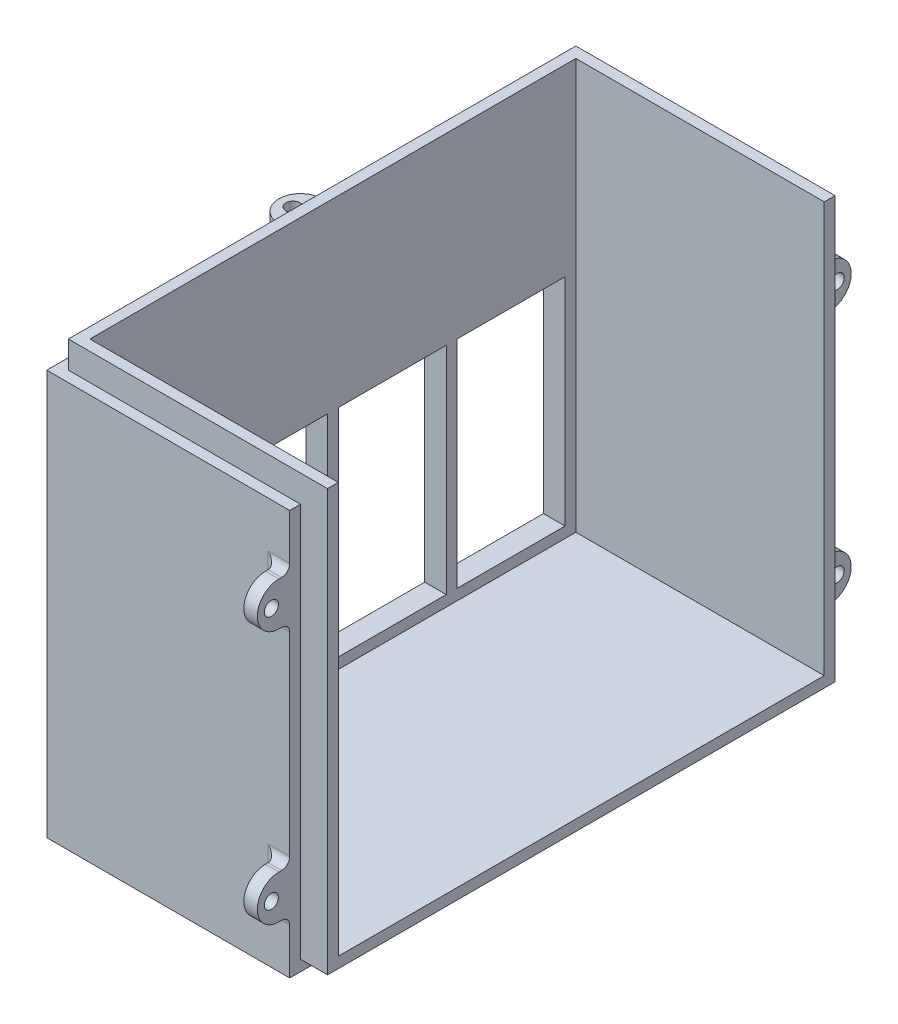
SolidWorks part; units mm, degrees
ref_plane "Front Plane" through (0, 0, 0) normal (0, 0, 1) x (1, 0, 0)
ref_plane "Top Plane" through (0, 0, 0) normal (0, 1, 0) x (1, 0, 0)
ref_plane "Right Plane" through (0, 0, 0) normal (1, 0, 0) x (0, 0, -1)
sketch "Sketch1" plane through (0, 0, 0) normal (0, 1, 0) x (1, 0, 0)
  line L1 (-25, 49) -> (25, 49)
  line L2 (-25, 49) -> (-25, -49)
  line L3 (-25, -49) -> (25, -49)
  line L4 (25, 49) -> (25, -49)
  line L5 (-25, 49) -> (25, -49) construction
  line L6 (-25, -49) -> (25, 49) construction
  point P0 (0, 0)
  dimension "D1" = 98
  dimension "D2" = 50
extrude "Boss-Extrude3" add sketch "Sketch1" along normal blind 80
sketch "Sketch4" plane through (25, 0, 0) normal (1, 0, 0) x (0, 0, -1)
  line L0 (-49, 80) -> (49, 80) construction
  line L1 (-45, 80) -> (45, 80)
  line L2 (-45, 80) -> (-45, 4)
  line L3 (-45, 4) -> (45, 4)
  line L4 (45, 80) -> (45, 4)
  line L5 (-49, 80) -> (-49, 0) construction
  line L6 (-49, 0) -> (49, 0) construction
  line L7 (49, 80) -> (49, 0) construction
  dimension "D1" = 4
  dimension "D2" = 4
  dimension "D3" = 4
extrude "Cut-Extrude2" cut sketch "Sketch4" against normal blind 46
sketch "Sketch6" plane through (0, 80, 0) normal (0, 1, 0) x (1, 0, 0)
  line L0 (-25, 49) -> (-25, -49) construction
  line L1 (25, -49) -> (-25, -49)
  line L2 (25, -49) -> (25, -47)
  line L3 (25, -47) -> (-25, -47)
  line L4 (-25, -49) -> (-25, -47)
  line L5 (25, 49) -> (-25, 49) construction
  line L6 (-25, -47) -> (-23, -47)
  line L7 (-25, -47) -> (-25, 49)
  line L8 (-25, 49) -> (-23, 49)
  line L9 (-23, -47) -> (-23, 49)
  line L10 (25, 45) -> (25, 49) construction
  line L11 (-23, 49) -> (25, 49)
  line L12 (-23, 49) -> (-23, 47)
  line L13 (-23, 47) -> (25, 47)
  line L14 (25, 49) -> (25, 47)
  line M9 (25, 45) -> (25, 49)
  line M10 (25, 49) -> (-25, 49)
  line M11 (-25, 49) -> (-25, -49)
  line M12 (-25, -49) -> (25, -49)
  line M13 (25, -49) -> (25, -45)
  dimension "D1" = 2
  dimension "D2" = 2
extrude "Cut-Extrude3" cut sketch "Sketch6" against normal blind 5 contours L9 L13 M9 M10 | L3 L9 M10 M11 | L3 M13 M11 M12
sketch "Sketch7" plane through (25, 0, 0) normal (1, 0, 0) x (0, 0, -1)
  line L0 (-49, 0) -> (49, 0) construction
  line L1 (-49, 75) -> (-47, 75)
  line L2 (-49, 75) -> (-49, 0)
  line L3 (-49, 0) -> (-47, 0)
  line L4 (-47, 75) -> (-47, 0)
  line L5 (-47, 75) -> (-47, 80) construction
  line L6 (49, 75) -> (49, 0) construction
  line L7 (-47, 0) -> (49, 0)
  line L8 (-47, 0) -> (-47, 2)
  line L9 (-47, 2) -> (49, 2)
  line L10 (49, 0) -> (49, 2)
  line L12 (49, 2) -> (47, 2)
  line L13 (49, 2) -> (49, 75)
  line L14 (49, 75) -> (47, 75)
  line L15 (47, 2) -> (47, 75)
  line M7 (-49, 0) -> (49, 0)
  line M8 (49, 0) -> (49, 75)
  line M9 (49, 75) -> (47, 75)
  dimension "D1" = 0
  dimension "D2" = 2
extrude "Cut-Extrude4" cut sketch "Sketch7" against normal blind 5 contours L9 L4 M7 M8 | L15 L9 M8 M9
sketch "Sketch10" plane through (20, 0, 0) normal (1, 0, 0) x (0, 0, -1)
  line L0 (-49, 75) -> (-49, 0) construction
  line L1 (-49, 10) -> (-51, 10)
  line L2 (-49, 10) -> (-49, 18)
  line L3 (-49, 18) -> (-51, 18)
  line L5 (-49, 0) -> (49, 0) construction
  line L6 (-49, 37.5) -> (-64.4145, 37.5) construction
  line L7 (-49, 65) -> (-49, 57)
  line L8 (-49, 65) -> (-51, 65)
  line L9 (-49, 57) -> (-51, 57)
  line L10 (0, 18) -> (0, 46) construction
  line L11 (49, 10) -> (49, 18)
  line L12 (49, 10) -> (51, 10)
  line L13 (49, 18) -> (51, 18)
  line L14 (49, 65) -> (51, 65)
  line L15 (49, 57) -> (51, 57)
  line L16 (49, 65) -> (49, 57)
  arc A0 (-51, 18) -> (-51, 10) centre (-51, 14) ccw
  circle A1 centre (-52.4, 14) radius 1.3
  circle A2 centre (-52.4, 61) radius 1.3
  arc A3 (-51, 57) -> (-51, 65) centre (-51, 61) cw
  circle A4 centre (52.4, 61) radius 1.3
  circle A5 centre (52.4, 14) radius 1.3
  arc A6 (51, 18) -> (51, 10) centre (51, 14) cw
  arc A7 (51, 57) -> (51, 65) centre (51, 61) ccw
  dimension "D4" = 2.6
  dimension "D1" = 10
  dimension "D2" = 8
  dimension "D3" = 2
  dimension "D5" = 3.4
extrude "Boss-Extrude6" add sketch "Sketch10" against normal blind 2.5
fillet "Fillet2" radius 1.5 6 edges at (18.75, 57, 49) (18.75, 65, 49) (17.5, 61, 49) (18.75, 18, 49) (17.5, 14, 49) (18.75, 10, 49)
fillet "Fillet3" radius 1.5 6 edges at (18.75, 65, -49) (17.5, 61, -49) (18.75, 57, -49) (18.75, 18, -49) (18.75, 10, -49) (17.5, 14, -49)
sketch "Sketch12" plane through (0, 75, 0) normal (0, 1, 0) x (1, 0, 0)
  line L0 (-25, 49) -> (-25, -49) construction
  line L1 (-25, 4) -> (-27, 4)
  line L2 (-25, 4) -> (-25, -4)
  line L3 (-25, -4) -> (-27, -4)
  line L5 (20, 49) -> (-25, 49) construction
  arc A0 (-27, 4) -> (-27, -4) centre (-27, 0) ccw
  circle A1 centre (-28.4, 0) radius 1.3
  dimension "D4" = 2.6
  dimension "D1" = 2
  dimension "D2" = 8
  dimension "D3" = 45
  dimension "D5" = 3.4
extrude "Boss-Extrude7" add sketch "Sketch12" against normal blind 2.5
fillet "Fillet4" radius 1.5 3 edges at (-25, 73.75, 4) (-25, 73.75, -4) (-25, 72.5, 0)
sketch "Sketch14" plane through (-25, 0, 0) normal (-1, 0, 0) x (0, 0, 1)
  line L0 (-49, 0) -> (49, 0) construction
  line L1 (23, 46) -> (43, 46)
  line L2 (23, 46) -> (23, 6)
  line L3 (23, 6) -> (43, 6)
  line L4 (43, 46) -> (43, 6)
  line L5 (1, 46) -> (21, 46)
  line L6 (1, 46) -> (1, 6)
  line L7 (1, 6) -> (21, 6)
  line L8 (21, 46) -> (21, 6)
  line L9 (-21, 46) -> (-1, 46)
  line L10 (-21, 46) -> (-21, 6)
  line L11 (-21, 6) -> (-1, 6)
  line L12 (-1, 46) -> (-1, 6)
  line L13 (-43, 46) -> (-23, 46)
  line L14 (-43, 46) -> (-43, 6)
  line L15 (-43, 6) -> (-23, 6)
  line L16 (-23, 46) -> (-23, 6)
  line L17 (-49, 75) -> (-49, 0) construction
  line L18 (49, 75) -> (49, 0) construction
  dimension "D1" = 20
  dimension "D2" = 40
  dimension "D3" = 20
  dimension "D4" = 40
  dimension "D5" = 20
  dimension "D6" = 40
  dimension "D7" = 40
  dimension "D8" = 20
  dimension "D9" = 6
  dimension "D10" = 6
  dimension "D11" = 6
  dimension "D12" = 6
  dimension "D13" = 6
  dimension "D14" = 6
  dimension "D15" = 2
  dimension "D16" = 2
extrude "Cut-Extrude5" cut sketch "Sketch14" against normal up to next
